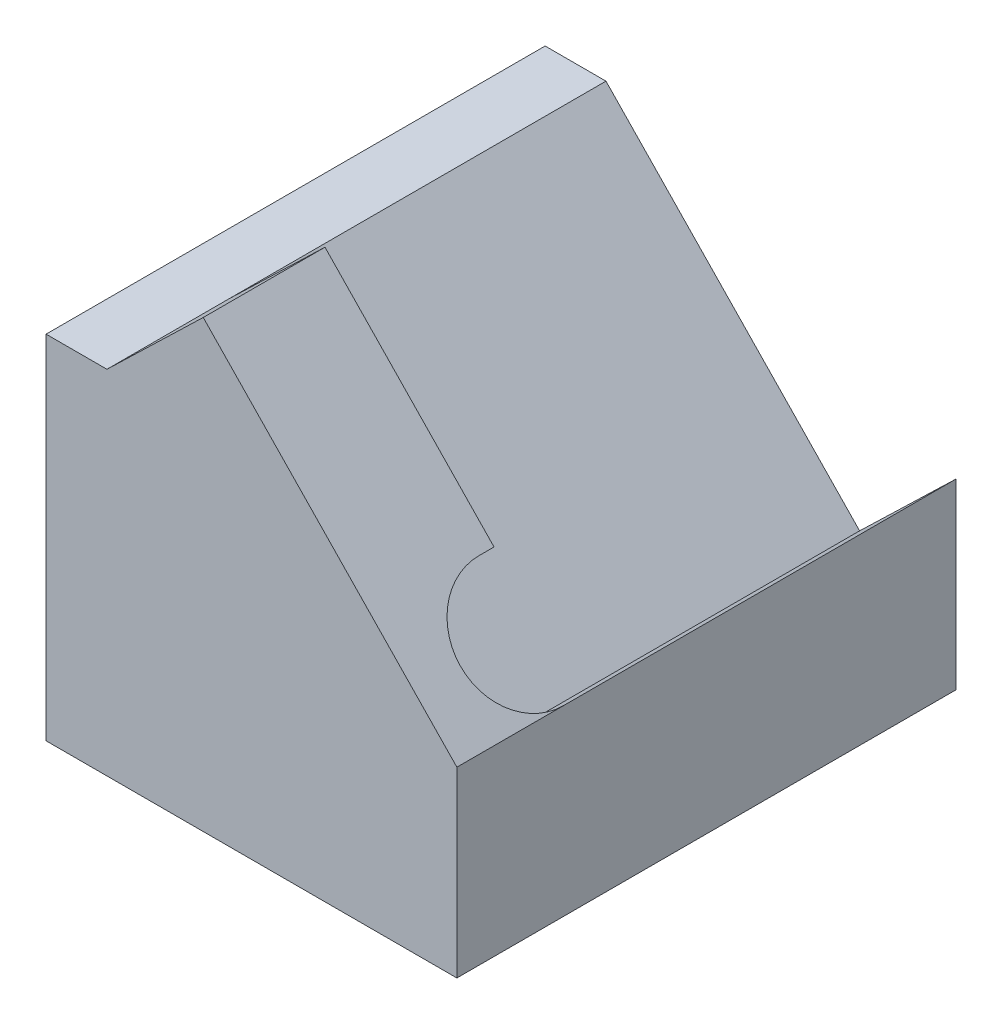
SolidWorks part; units mm, degrees
ref_plane "Front Plane" through (0, 0, 0) normal (0, 0, 1) x (1, 0, 0)
ref_plane "Top Plane" through (0, 0, 0) normal (0, 1, 0) x (1, 0, 0)
ref_plane "Right Plane" through (0, 0, 0) normal (1, 0, 0) x (0, 0, -1)
sketch "Sketch1" plane through (0, 0, 0) normal (0, 0, 1) x (1, 0, 0)
  line L0 (0, 0) -> (0, 4.7873)
  line L1 (0, 4.7873) -> (1, 4.7873)
  line L2 (1, 4.7873) -> (2.5825, 6.3155)
  line L3 (2.5825, 6.3155) -> (6.75, 2)
  line L4 (6.75, 2) -> (6.75, 0)
  line L5 (6.75, 0) -> (0, 0)
  dimension "D1" = 2
  dimension "D2" = 6.75
  dimension "D3" = 136
  dimension "D4" = 2.2
  dimension "D5" = 1
extrude "Boss-Extrude1" add sketch "Sketch1" along normal blind 8.2
sketch "Sketch2" plane through (4.4922, 4.338, 0) normal (0.7193, 0.6947, 0) x (0, 0, -1)
  line L0 (0, -3.2503) -> (-6.45, -3.2503)
  line L1 (-8.2, -3.2503) -> (0, -3.2503) construction
  line L2 (-6.45, -1.2503) -> (-6.2, -1.2503)
  line L3 (-6.2, -1.2503) -> (-6.2, 3.2497)
  line L4 (-6.2, 3.2497) -> (0, 3.2497)
  line L5 (0, 2.749) -> (0, 3.4437) construction
  line L6 (0, 3.2497) -> (0, -3.2503)
  arc A0 (-6.45, -3.2503) -> (-6.45, -1.2503) centre (-6.45, -2.2503) cw
  dimension "D1" = 6.5
  dimension "D2" = 6.2
  dimension "D3" = 0.25
  dimension "D4" = 2
extrude "Cut-Extrude1" cut sketch "Sketch2" against normal blind 2.2
sketch "Sketch7" plane through (0, 0, 0) normal (0, -1, 0) x (1, 0, 0)
  line L1 (0, 8.2) -> (6.75, 8.2)
  line L2 (0, 8.2) -> (0, 0)
  line L3 (0, 0) -> (6.75, 0)
  line L4 (6.75, 8.2) -> (6.75, 0)
extrude "Boss-Extrude2" add sketch "Sketch7" along normal blind 1
hole_wizard "Ø1.5mm Dowel Hole1" positions "Sketch4" profile "Sketch3" hole size "Ø1.5" standard "ISO"
sketch "Sketch4" plane through (0, -1, 0) normal (0, -1, 0) x (-1, 0, 0)
  line L0 (0, -8.2) -> (0, 0) construction
  line L2 (0, -8.2) -> (0, 0) construction
  point P0 (-3, -7.1)
  point P2 (-3, -1.1)
  point P5 (0, -4.1)
  dimension "D1" = 6
  dimension "D2" = 3
  dimension "D3" = 3
sketch "Sketch3" plane through (3, -1, 7.1) normal (1, 0, 0) x (0, 0, -1)
  line L0 (0, 0) -> (0, 1.9506)
  line L1 (0, 1.9506) -> (0.75, 1.5)
  line L2 (0.75, 1.5) -> (0.75, 0)
  line L5 (0.75, 0) -> (0, 0)
  line L10 (0, 1.9506) -> (-0.75, 1.5) construction
  line L11 (0, -6.35) -> (0, 107.95) construction
  dimension "Hole Dia." = 1.5
  dimension "Hole Depth" = 1.5
  dimension "Drill Angle" = 118
hole_wizard "M2x0.4 Tapped Hole1" positions "Sketch6" profile "Sketch5" tap size "M2x0.4" standard "ANSI Metric"
sketch "Sketch6" plane through (0, -1, 0) normal (0, -1, 0) x (-1, 0, 0)
  line L2 (0, -8.2) -> (0, 0) construction
  line L3 (0, 0) -> (-6.75, 0) construction
  point P0 (-3, -4.1)
  dimension "D1" = 3
  dimension "D2" = 4.1
sketch "Sketch5" plane through (3, -1, 4.1) normal (1, 0, 0) x (0, 0, -1)
  line L0 (0, 0) -> (0, 2.9807)
  line L1 (0, 2.9807) -> (0.8, 2.5)
  line L2 (0.8, 2.5) -> (0.8, 0)
  line L5 (0.8, 0) -> (0, 0)
  line L10 (0, 2.9807) -> (-0.8, 2.5) construction
  line L11 (0, -6.35) -> (0, 107.95) construction
  dimension "Tap Drill Dia." = 1.6
  dimension "Tap Drill Depth" = 2.5
  dimension "Drill Angle" = 118
cosmetic thread "Hole Thread2" parameters "D1"=2.5, "D2"=2
